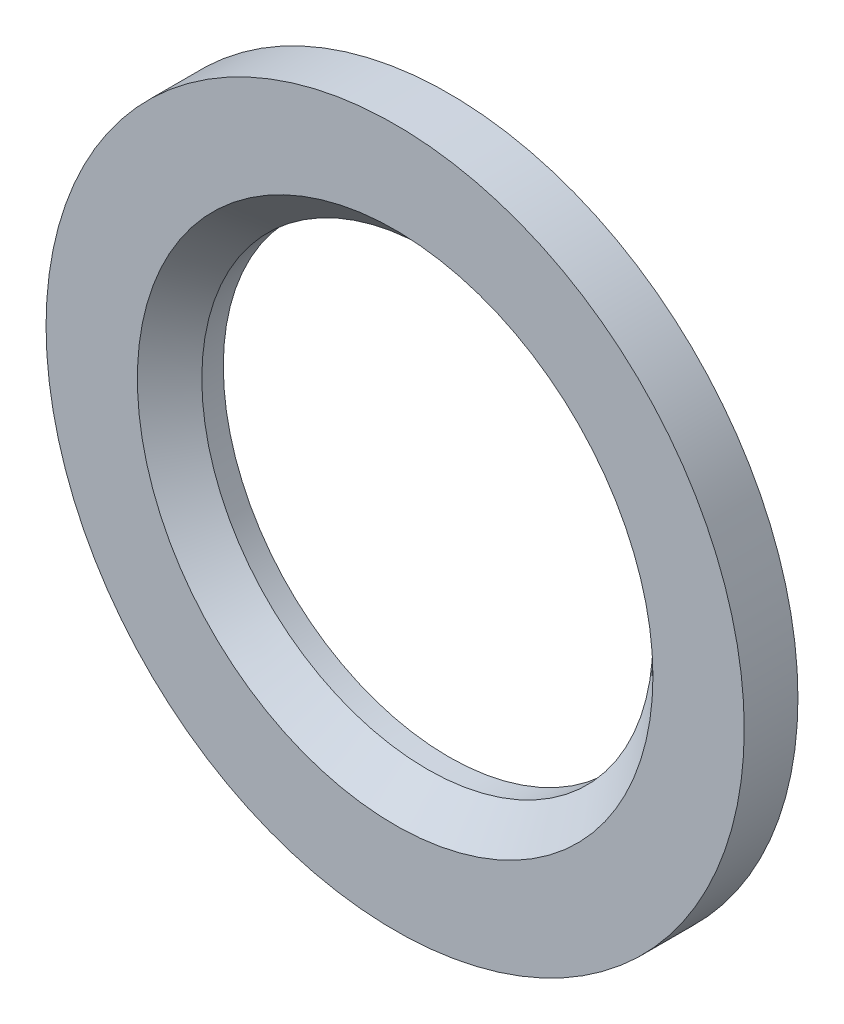
SolidWorks part; units mm, degrees
ref_plane "Front Plane" through (0, 0, 0) normal (0, 0, 1) x (1, 0, 0)
ref_plane "Top Plane" through (0, 0, 0) normal (0, 1, 0) x (1, 0, 0)
ref_plane "Right Plane" through (0, 0, 0) normal (1, 0, 0) x (0, 0, -1)
sketch "Sketch1" plane through (0, 0, 0) normal (0, 0, 1) x (1, 0, 0)
  circle A0 centre (0, 0) radius 4.2
  circle A1 centre (0, 0) radius 6.5
  dimension "D1" = 8.4
  dimension "D2" = 13
extrude "Boss-Extrude1" add sketch "Sketch1" along normal blind 1
chamfer "Chamfer1" distance 0.6 angle 45 1 edges at (4.2, 0, 1)
